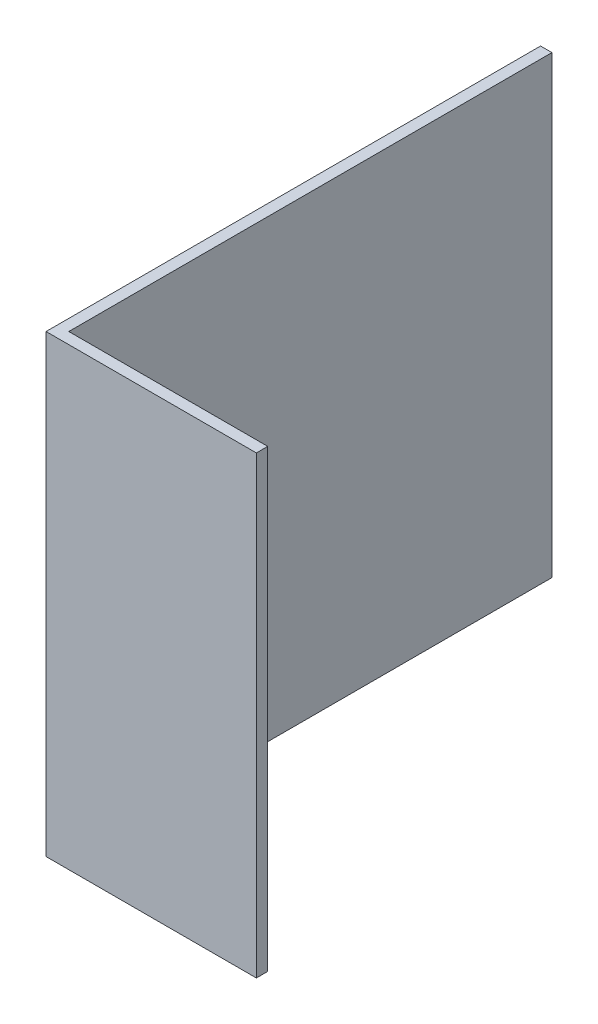
SolidWorks part; units mm, degrees
ref_plane "前视基准面" through (0, 0, 0) normal (0, 0, 1) x (1, 0, 0)
ref_plane "上视基准面" through (0, 0, 0) normal (0, 1, 0) x (1, 0, 0)
ref_plane "右视基准面" through (0, 0, 0) normal (1, 0, 0) x (0, 0, -1)
sketch "草图1" plane through (0, 0, 0) normal (0, 1, 0) x (1, 0, 0)
  line L0 (0, 0) -> (0, 87)
  line L1 (0, 87) -> (-2, 87)
  line L2 (-2, 87) -> (-2, 0)
  line L3 (-2, 0) -> (0, 0)
  dimension "D1" = 2
  dimension "D2" = 87
extrude "凸台-拉伸1" add sketch "草图1" along normal mid plane 80
sketch "草图2" plane through (0, 0, 0) normal (1, 0, 0) x (0, 0, -1)
  line L0 (2, 40) -> (0, 40)
  line L2 (0, 40) -> (0, -40)
  line L3 (0, -40) -> (2, -40)
  line L4 (0, -40) -> (87, -40) construction
  line L5 (2, -40) -> (2, 40)
  dimension "D1" = 2
extrude "凸台-拉伸2" add sketch "草图2" along normal blind 35
